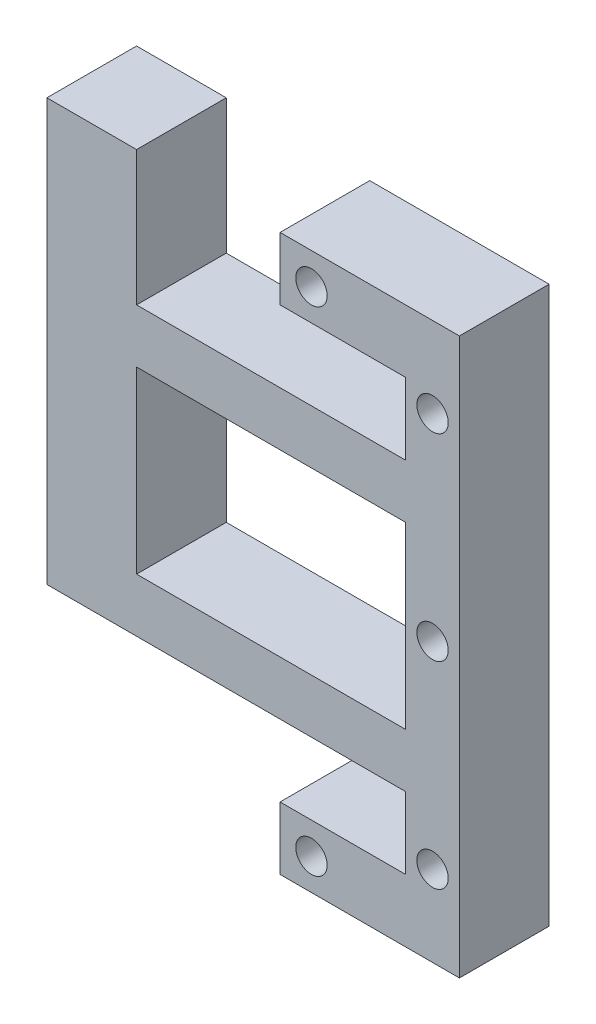
SolidWorks part; units mm, degrees
ref_plane "Front Plane" through (0, 0, 0) normal (0, 0, 1) x (1, 0, 0)
ref_plane "Top Plane" through (0, 0, 0) normal (0, 1, 0) x (1, 0, 0)
ref_plane "Right Plane" through (0, 0, 0) normal (1, 0, 0) x (0, 0, -1)
sketch "Sketch1" plane through (0, 0, 0) normal (0, 0, 1) x (1, 0, 0)
  line L0 (-2.4196, 1) -> (11, 1)
  line L1 (11, 1) -> (11, 8)
  line L26 (5, 56) -> (5, 8)
  line L27 (5, 8) -> (-9, 8)
  line L28 (-9, 8) -> (-9, 1)
  line L29 (-9, 1) -> (-2.4196, 1)
  line L35 (11, 8) -> (11, 63)
  line L36 (11, 63) -> (-9, 63)
  line L37 (-9, 63) -> (-9, 56)
  line L38 (-9, 56) -> (5, 56)
  circle A0 centre (-5.5, 59.5) radius 1.75
  circle A1 centre (8, 54) radius 1.75
  circle A2 centre (-5.5, 4.5) radius 1.75
  circle A3 centre (8, 10) radius 1.75
  circle A4 centre (8, 32) radius 1.75
extrude "Boss-Extrude1" add sketch "Sketch1" along normal blind 10
sketch "Sketch2" plane through (0, 0, 10) normal (0, 0, 1) x (1, 0, 0)
  line L10 (5, 56) -> (5, 8) construction
  line L15 (5, 48) -> (-35, 48)
  line L16 (5, 48) -> (5, 42)
  line L17 (5, 42) -> (-35, 42)
  line L18 (-35, 48) -> (-35, 42)
  line L19 (-9, 56) -> (5, 56) construction
  line L20 (5, 22) -> (-35, 22)
  line L21 (5, 22) -> (5, 16)
  line L22 (5, 16) -> (-35, 16)
  line L23 (-35, 22) -> (-35, 16)
  line L24 (5, 8) -> (-9, 8) construction
  line L25 (11, 63) -> (-9, 63) construction
  line L26 (-35, 16) -> (-25, 16)
  line L27 (-35, 16) -> (-35, 63)
  line L28 (-35, 63) -> (-25, 63)
  line L29 (-25, 16) -> (-25, 63)
  dimension "D1" = 8
  dimension "D2" = 6
  dimension "D3" = 8
  dimension "D4" = 6
  dimension "D5" = 40
  dimension "D6" = 10
extrude "Boss-Extrude2" add sketch "Sketch2" against normal up to surface (10 mm away) up to face at (9.75, 10, 0)
